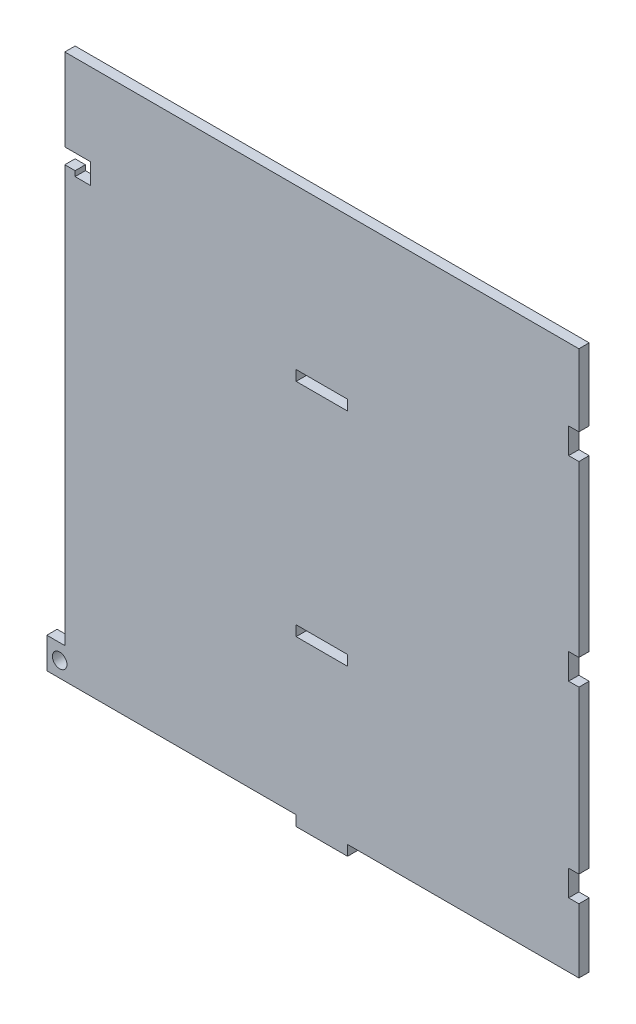
SolidWorks part; units mm, degrees
ref_plane "Front Plane" through (0, 0, 0) normal (0, 0, 1) x (1, 0, 0)
ref_plane "Top Plane" through (0, 0, 0) normal (0, 1, 0) x (1, 0, 0)
ref_plane "Right Plane" through (0, 0, 0) normal (1, 0, 0) x (0, 0, -1)
sketch "Sketch1" plane through (0, 0, 0) normal (0, 0, 1) x (1, 0, 0)
  line L0 (-50, 0) -> (-5, 0)
  line L1 (-5, 0) -> (-5, -2)
  line L2 (-5, -2) -> (5, -2)
  line L3 (5, -2) -> (5, 0)
  line L4 (5, 0) -> (50, 0)
  line L5 (-5, 0) -> (5, 0)
  line L6 (50, 0) -> (50, 12.5)
  line L7 (50, 12.5) -> (48, 12.5)
  line L8 (48, 12.5) -> (48, 17.5)
  line L9 (48, 17.5) -> (50, 17.5)
  line L10 (50, 17.5) -> (50, 30)
  line L11 (50, 49) -> (48, 49)
  line L12 (48, 49) -> (48, 54)
  line L13 (48, 54) -> (50, 54)
  line L14 (50, 30) -> (50, 49)
  line L15 (-50, 106) -> (50, 106)
  line L20 (-50, 87) -> (-48, 87)
  line L21 (-50, 30) -> (50, 30) construction
  line L22 (-50, 73) -> (50, 73) construction
  line L23 (-5, 0) -> (-5, 38.3205) construction
  line L24 (-5, 32) -> (5, 32)
  line L25 (-5, 32) -> (-5, 30)
  line L26 (-5, 30) -> (5, 30)
  line L27 (5, 32) -> (5, 30)
  line L28 (-5, 75) -> (5, 75)
  line L29 (-5, 75) -> (-5, 73)
  line L30 (-5, 73) -> (5, 73)
  line L31 (5, 75) -> (5, 73)
  line L34 (50, 54) -> (50, 73)
  line L35 (50, 73) -> (50, 87)
  line L36 (50, 87) -> (48, 87)
  line L37 (48, 87) -> (48, 92)
  line L38 (48, 92) -> (50, 92)
  line L39 (50, 92) -> (50, 106)
  line L40 (-45, 87) -> (-45, 90)
  line L41 (-45, 90) -> (-50, 90)
  line L42 (-50, 90) -> (-50, 106)
  line L43 (-50, 6) -> (-50, 87)
  line L44 (-50, 0) -> (-53.5, 0)
  line L45 (-53.5, 0) -> (-53.5, 6)
  line L46 (-53.5, 6) -> (-50, 6)
  line L47 (-50, 6) -> (-50, 0) construction
  line L48 (-48, 87) -> (-48, 86)
  line L49 (-52, 4) -> (-50, 4) construction
  line L50 (-52, 4) -> (-52, 2) construction
  line L51 (-52, 2) -> (-50, 2) construction
  line L52 (-50, 4) -> (-50, 2) construction
  line L53 (-48, 86) -> (-45, 86)
  line L54 (-45, 86) -> (-45, 87)
  circle A0 centre (-51, 3) radius 1.4142
  dimension "D8" = 2
  dimension "D11" = 3
  dimension "D1" = 100
  dimension "D2" = 2
  dimension "D3" = 10
  dimension "D4" = 5
  dimension "D5" = 30
  dimension "D6" = 41
  dimension "D7" = 100
  dimension "D9" = 3.5
  dimension "D10" = 6
  dimension "D12" = 31
  dimension "D13" = 10
  dimension "D14" = 3
  dimension "D15" = 16
  dimension "D16" = 1
  dimension "D17" = 3
  dimension "D18" = 1
  dimension "D19" = 2
  dimension "D20" = 2
extrude "Boss-Extrude1" add sketch "Sketch1" along normal blind 2
